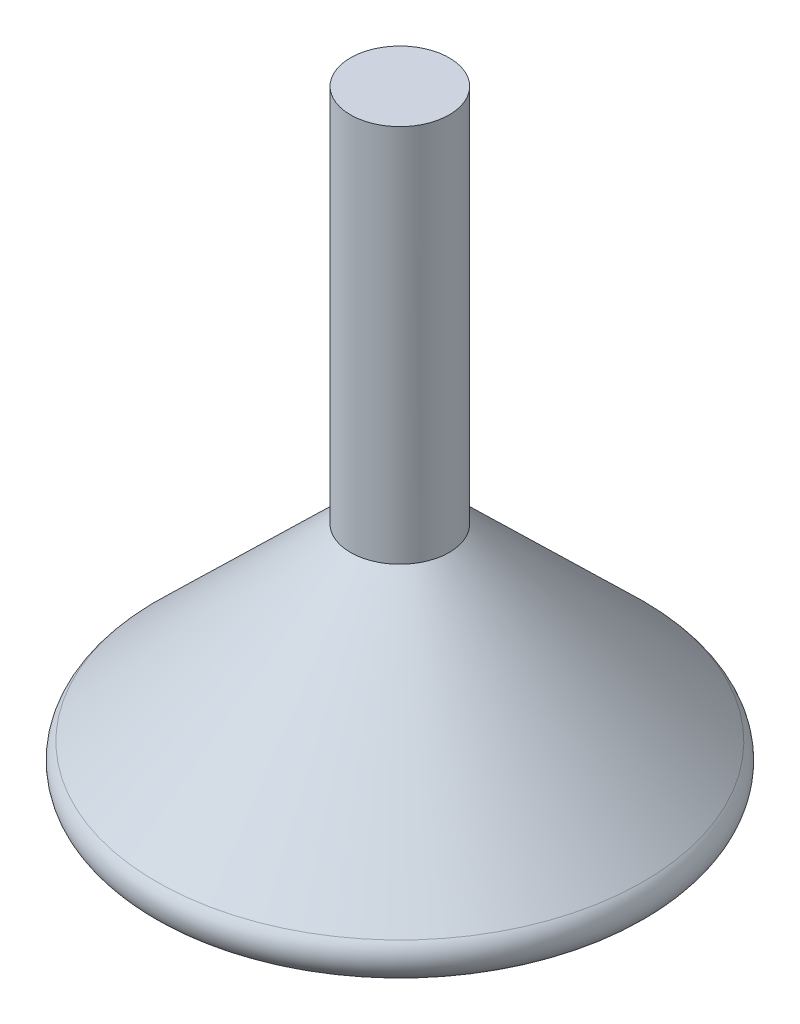
SolidWorks part; units mm, degrees
ref_plane "Front Plane" through (0, 0, 0) normal (0, 0, 1) x (1, 0, 0)
ref_plane "Top Plane" through (0, 0, 0) normal (0, 1, 0) x (1, 0, 0)
ref_plane "Right Plane" through (0, 0, 0) normal (1, 0, 0) x (0, 0, -1)
sketch "Sketch1" plane through (0, 0, 0) normal (0, 0, 1) x (1, 0, 0)
  line L0 (0, 0) -> (0, 30) construction
  line L1 (32.0906, 5.1516) -> (6.5164, 30)
  line L2 (0, 0) -> (0, 30)
  line L3 (30, 0) -> (0, 0)
  line L4 (6.5164, 30) -> (0, 30)
  line L5 (0, 27.6229) -> (0, 77.1394) construction
  arc A0 (32.0906, 5.1516) -> (30, 0) centre (30, 3) cw
  dimension "D1" = 3
  dimension "D2" = 30
  dimension "D3" = 30
revolve "Revolve1" add sketch "Sketch1" angle 360 about L5
sketch "Sketch2" plane through (0, 30, 0) normal (0, 1, 0) x (1, 0, 0)
  circle A0 centre (0, 0) radius 6.5164
extrude "Boss-Extrude1" add sketch "Sketch2" along normal blind 50
